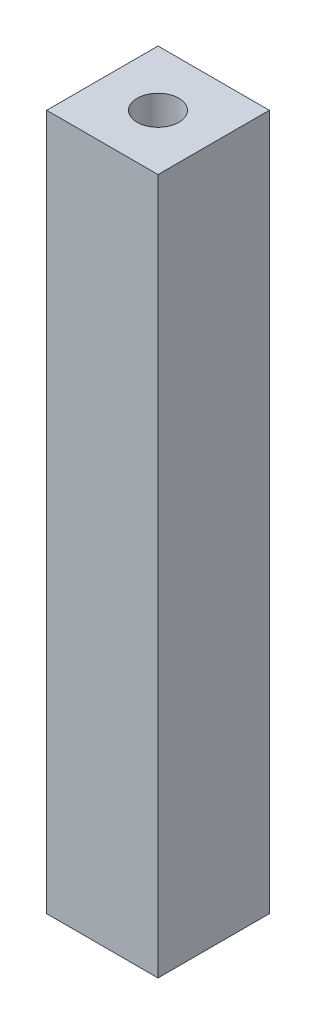
SolidWorks part; units mm, degrees
ref_plane "Front Plane" through (0, 0, 0) normal (0, 0, 1) x (1, 0, 0)
ref_plane "Top Plane" through (0, 0, 0) normal (0, 1, 0) x (1, 0, 0)
ref_plane "Right Plane" through (0, 0, 0) normal (1, 0, 0) x (0, 0, -1)
sketch "Sketch1" plane through (0, 0, 0) normal (0, 1, 0) x (1, 0, 0)
  line L1 (-4, -4) -> (4, -4)
  line L2 (-4, -4) -> (-4, 4)
  line L3 (-4, 4) -> (4, 4)
  line L4 (4, -4) -> (4, 4)
  line L5 (-4, -4) -> (4, 4) construction
  line L6 (-4, 4) -> (4, -4) construction
  point P0 (0, 0)
  dimension "D1" = 8
extrude "Boss-Extrude1" add sketch "Sketch1" along normal blind 50
sketch "Sketch2" plane through (0, 50, 0) normal (0, 1, 0) x (1, 0, 0)
  circle A0 centre (0, 0) radius 1.5
  dimension "D1" = 3
extrude "Cut-Extrude1" cut sketch "Sketch2" against normal through all
